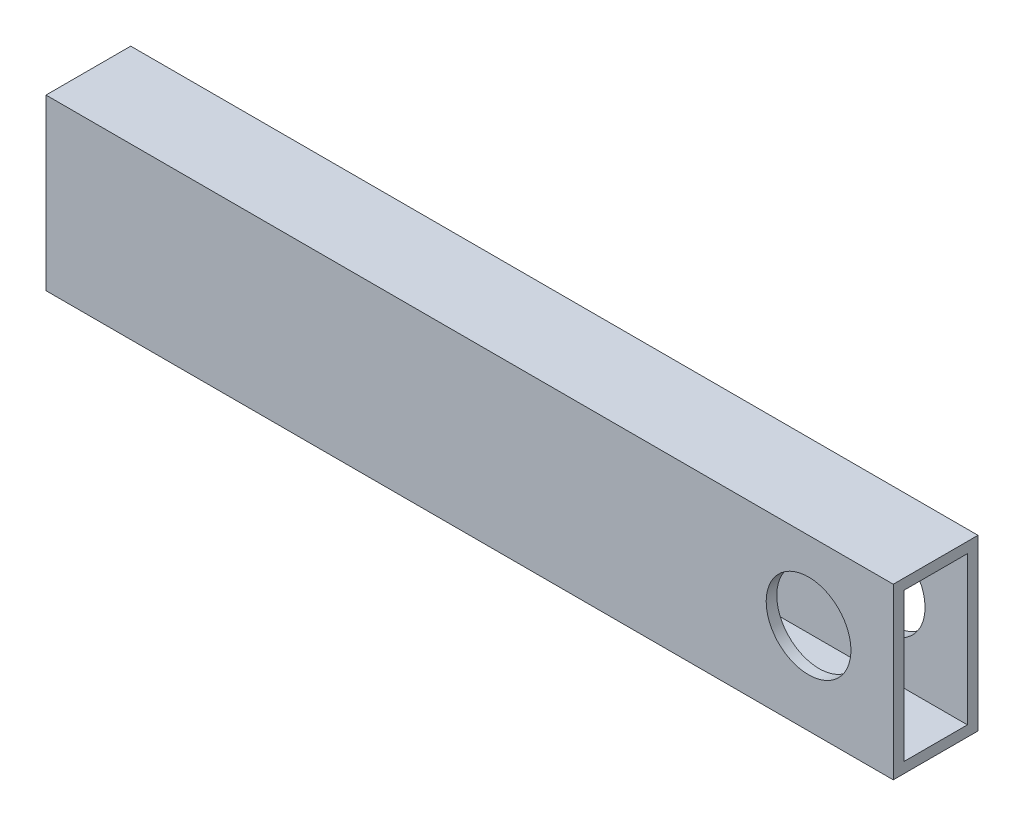
SolidWorks part; units mm, degrees
ref_plane "Front Plane" through (0, 0, 0) normal (0, 0, 1) x (1, 0, 0)
ref_plane "Top Plane" through (0, 0, 0) normal (0, 1, 0) x (1, 0, 0)
ref_plane "Right Plane" through (0, 0, 0) normal (1, 0, 0) x (0, 0, -1)
sketch "Sketch1" plane through (0, 0, 0) normal (1, 0, 0) x (0, 0, -1)
  line L1 (0, 0) -> (25.4, 0)
  line L2 (0, 0) -> (0, 50.8)
  line L3 (0, 50.8) -> (25.4, 50.8)
  line L4 (25.4, 0) -> (25.4, 50.8)
  line L5 (3.175, 47.625) -> (22.225, 47.625)
  line L6 (3.175, 47.625) -> (3.175, 3.175)
  line L7 (3.175, 3.175) -> (22.225, 3.175)
  line L8 (22.225, 47.625) -> (22.225, 3.175)
  dimension "D1" = 3.175
  dimension "D2" = 3.175
  dimension "D3" = 3.175
  dimension "D4" = 3.175
  dimension "D5" = 50.8
  dimension "D6" = 25.4
extrude "Boss-Extrude1" add sketch "Sketch1" along normal blind 304.8
sketch "Sketch2" plane through (0, 0, -25.4) normal (0, 0, -1) x (-1, 0, 0)
  line L0 (-304.8, 0) -> (-304.8, 50.8) construction
  circle A0 centre (-279.4, 27.2833) radius 12.7
  dimension "D2" = 25.4
  dimension "D1" = 25.4
extrude "Cut-Extrude1" cut sketch "Sketch2" against normal through all both and the other way through all
sketch "Sketch3" plane through (0, 0, -25.4) normal (0, 0, -1) x (-1, 0, 0)
  line L0 (0, 50.8) -> (-50.8, 50.8)
  line L1 (-304.8, 50.8) -> (0, 50.8) construction
  line L2 (-50.8, 50.8) -> (-50.8, -4.3124)
  line L3 (-50.8, -4.3124) -> (0, -4.3124)
  line L4 (0, -4.3124) -> (0, 50.8)
  dimension "D1" = 50.8
extrude "Cut-Extrude2" cut sketch "Sketch3" against normal blind 159.004
